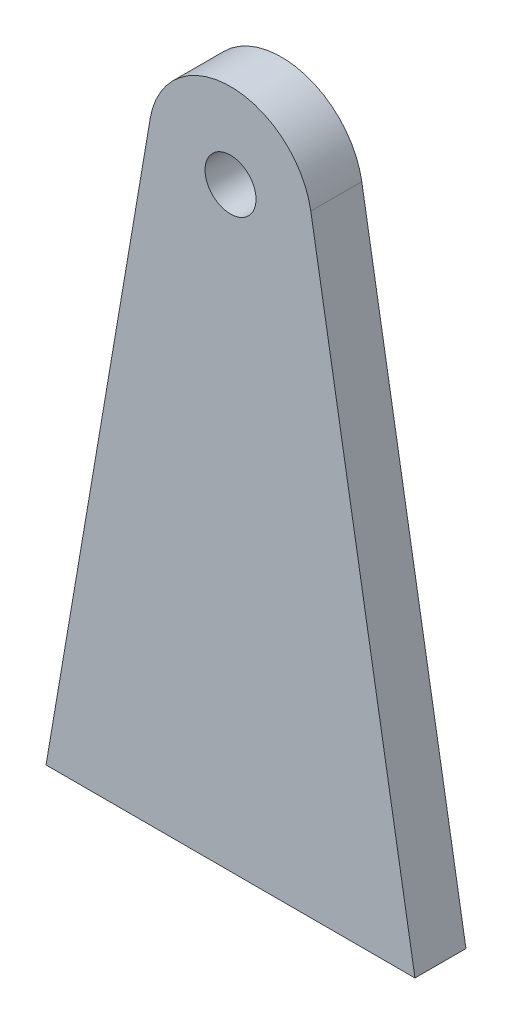
SolidWorks part; units mm, degrees
ref_plane "Спереди" through (0, 0, 0) normal (0, 0, 1) x (1, 0, 0)
ref_plane "Сверху" through (0, 0, 0) normal (0, 1, 0) x (1, 0, 0)
ref_plane "Справа" through (0, 0, 0) normal (1, 0, 0) x (0, 0, -1)
other "Configuration Table"
sketch "Sketch1" plane through (0, 0, 0) normal (0, 0, 1) x (1, 0, 0)
  line L0 (10.8536, -24.9058) -> (-10.8536, -24.9058)
  line L1 (-10.8536, -24.9058) -> (-4.7238, 11.1065)
  line L2 (0, -2.5384) -> (0, 6.0579) construction
  line L3 (10.8536, -24.9058) -> (4.7238, 11.1065)
  arc A0 (-4.7238, 11.1065) -> (0, 15.0942) centre (0, 10.3025) cw
  arc A1 (4.7238, 11.1065) -> (0, 15.0942) centre (0, 10.3025) ccw
  circle A2 centre (0, 10.0942) radius 1.5
  point P11 (0, -24.9058)
  dimension "D1" = 3
  dimension "D2" = 5
  dimension "D3" = 40
extrude "Boss-Extrude1" add sketch "Sketch1" along normal blind 3
